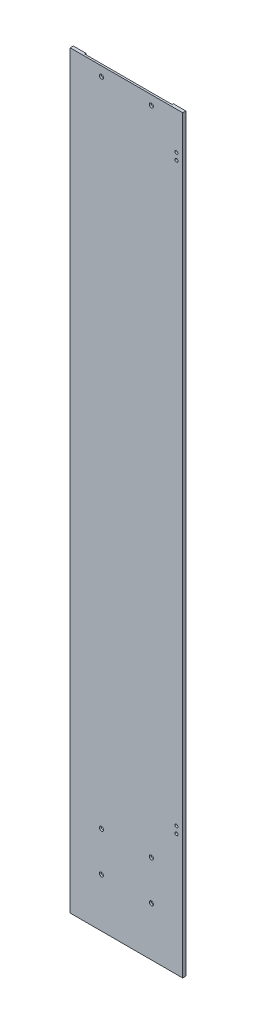
SolidWorks part; units mm, degrees
ref_plane "Front Plane" through (0, 0, 0) normal (0, 0, 1) x (1, 0, 0)
ref_plane "Top Plane" through (0, 0, 0) normal (0, 1, 0) x (1, 0, 0)
ref_plane "Right Plane" through (0, 0, 0) normal (1, 0, 0) x (0, 0, -1)
sketch "Sketch1" plane through (0, 0, 0) normal (0, 0, 1) x (1, 0, 0)
  line L1 (-90, 600) -> (90, 600)
  line L2 (-90, 600) -> (-90, -600)
  line L3 (-90, -600) -> (90, -600)
  line L4 (90, 600) -> (90, -600)
  line L5 (-90, 600) -> (90, -600) construction
  line L6 (-90, -600) -> (90, 600) construction
  point P0 (0, 0)
  dimension "D1" = 180
  dimension "D2" = 1200
extrude "Boss-Extrude1" add sketch "Sketch1" along normal blind 5
sketch "Sketch2" plane through (0, 0, 0) normal (0, 0, -1) x (-1, 0, 0)
  line L0 (-90, 600) -> (90, 600) construction
  line L1 (-70, 600) -> (70, 600)
  line L2 (-70, 600) -> (-70, -600)
  line L3 (-70, -600) -> (70, -600)
  line L4 (70, 600) -> (70, -600)
  line L5 (-70, 600) -> (70, -600) construction
  line L6 (-70, -600) -> (70, 600) construction
  line L7 (90, -600) -> (-90, -600) construction
  line L8 (0, 499.8286) -> (0, 472.6641) construction
  line L9 (-90, 600) -> (90, -600) construction
  line L10 (-90, -600) -> (90, 600) construction
  point P4 (0, 0)
  dimension "D1" = 140
extrude "Cut-Extrude1" cut sketch "Sketch2" against normal blind 2
sketch "Sketch3" plane through (0, 0, 5) normal (0, 0, 1) x (1, 0, 0)
  line L0 (0, -600) -> (0, 600) construction
  line L1 (-90, -600) -> (90, -600) construction
  line L2 (90, 600) -> (-90, 600) construction
  line L3 (-40, -600) -> (-40, 600) construction
  line L4 (40, -600) -> (40, 600) construction
  circle A0 centre (-40, -521.5) radius 3.3
  circle A1 centre (-40, -458) radius 3.3
  circle A2 centre (-40, 585) radius 3.3
  circle A3 centre (40, 585) radius 3.3
  circle A4 centre (40, -458) radius 3.3
  circle A5 centre (40, -521.5) radius 3.3
  dimension "D1" = 6.6
  dimension "D2" = 15
  dimension "D4" = 1121.5
  dimension "D3" = 1058
  dimension "D5" = 40
extrude "Cut-Extrude2" cut sketch "Sketch3" against normal through all
sketch "Sketch4" plane through (0, 0, 0) normal (0, 0, -1) x (-1, 0, 0)
  line L0 (-90, 600) -> (-70, 600) construction
  line L2 (-80, -600) -> (-80, 600) construction
  line L3 (-70, -600) -> (-90, -600) construction
  circle A0 centre (-80, 539.95) radius 2.5
  circle A1 centre (-80, 529) radius 2.5
  circle A2 centre (-80, -394.05) radius 2.5
  circle A3 centre (-80, -405) radius 2.5
  point P14 (0, 0)
  point P15 (0, 0)
  dimension "D2" = 5
  dimension "D1" = 10.95
  dimension "D3" = 10.95
  dimension "D4" = 71
  dimension "D5" = 1005
extrude "Cut-Extrude3" cut sketch "Sketch4" against normal through all
